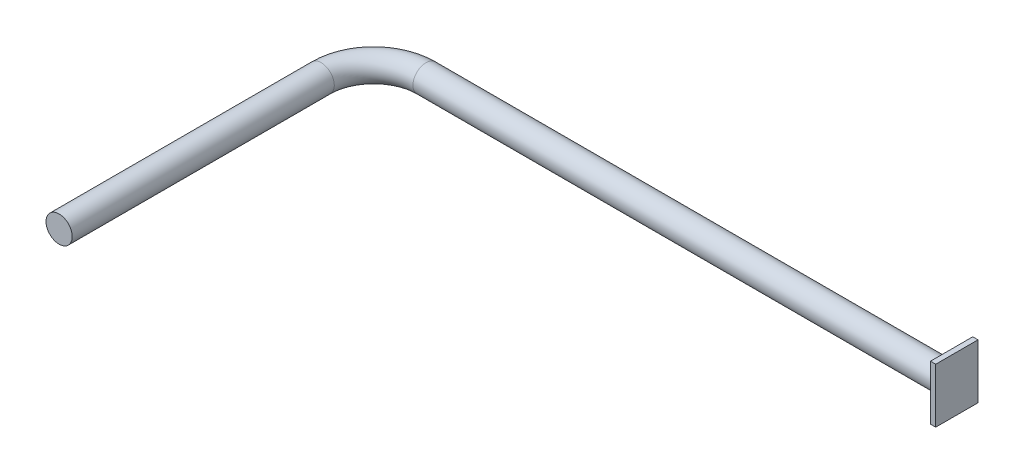
SolidWorks part; units mm, degrees
ref_plane "Front Plane" through (0, 0, 0) normal (0, 0, 1) x (1, 0, 0)
ref_plane "Top Plane" through (0, 0, 0) normal (0, 1, 0) x (1, 0, 0)
ref_plane "Right Plane" through (0, 0, 0) normal (1, 0, 0) x (0, 0, -1)
sketch "Sketch1" plane through (0, 0, 0) normal (0, 0, 1) x (1, 0, 0)
  circle A0 centre (0, 0) radius 25
  dimension "D1" = 50
sketch "Sketch3" plane through (0, 0, 0) normal (0, 1, 0) x (1, 0, 0)
  line L0 (0, 0) -> (0, 500)
  line L1 (100, 600) -> (1100, 600)
  arc A0 (0, 500) -> (100, 600) centre (100, 500) cw
  dimension "D3" = 100
  dimension "D1" = 1000
  dimension "D2" = 500
sweep "Sweep1" add profiles "Sketch1" path "Sketch3"
sketch "Sketch4" plane through (1100, 0, 0) normal (1, 0, 0) x (0, 0, -1)
  line L1 (562.4973, 50.5097) -> (643.1087, 50.5097)
  line L2 (562.4973, 50.5097) -> (562.4973, -53.5709)
  line L3 (562.4973, -53.5709) -> (643.1087, -53.5709)
  line L4 (643.1087, 50.5097) -> (643.1087, -53.5709)
extrude "Boss-Extrude1" add sketch "Sketch4" along normal blind 10
